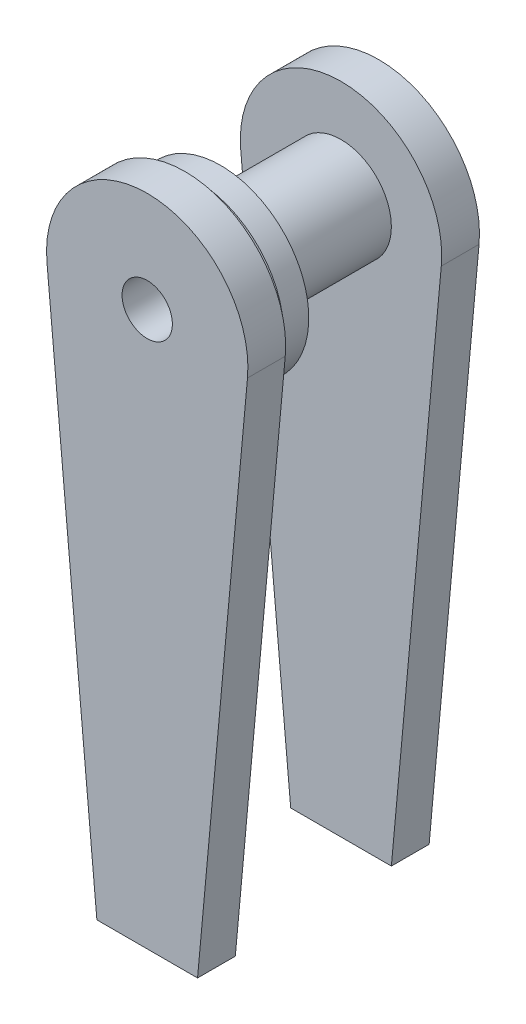
SolidWorks part; units mm, degrees
ref_plane "Front Plane" through (0, 0, 0) normal (0, 0, 1) x (1, 0, 0)
ref_plane "Top Plane" through (0, 0, 0) normal (0, 1, 0) x (1, 0, 0)
ref_plane "Right Plane" through (0, 0, 0) normal (1, 0, 0) x (0, 0, -1)
sketch "Sketch1" plane through (0, 0, 0) normal (0, 0, 1) x (1, 0, 0)
  line L0 (-25.2939, -2.3187) -> (-12.7, -139.7)
  line L1 (25.2939, -2.3187) -> (12.7, -139.7)
  line L2 (-12.7, -139.7) -> (12.7, -139.7)
  circle A0 centre (0, 0) radius 6.35
  circle A1 centre (0, 0) radius 25.4
  point P8 (12.1942, -139.7)
  point P11 (0, -25.4)
  dimension "D1" = 12.7
  dimension "D2" = 50.8
  dimension "D3" = 114.3
  dimension "D4" = 25.4
extrude "Boss-Extrude1" add sketch "Sketch1" along normal blind 9.525 contours A1 L0 L2 L1 | A1 A0
ref_plane "Plane1" through (0, 0, 29.21) normal (0, 0, -1) x (-1, 0, 0)
sketch "Sketch2" plane through (0, 0, 9.525) normal (0, 0, 1) x (1, 0, 0)
  circle A0 centre (0, 0) radius 6.35
  circle A1 centre (0, 0) radius 12.7
  dimension "D1" = 25.4
  dimension "D2" = 12.7
extrude "Boss-Extrude2" add sketch "Sketch2" along normal blind 39.37
mirror "Mirror2" about plane through (0, 0, 29.21) normal (0, 0, -1) of "Boss-Extrude1"
ref_plane "Plane2" through (0, 0, 39.878) normal (0, 0, -1) x (-1, 0, 0)
sketch "Sketch3" plane through (0, 0, 39.878) normal (0, 0, -1) x (-1, 0, 0)
  circle A0 centre (0, 0) radius 22.225
  circle A1 centre (0, 0) radius 12.7
  circle A3 centre (0, 0) radius 12.7 construction
  dimension "D1" = 44.45
extrude "Boss-Extrude3" add sketch "Sketch3" against normal blind 6.35
